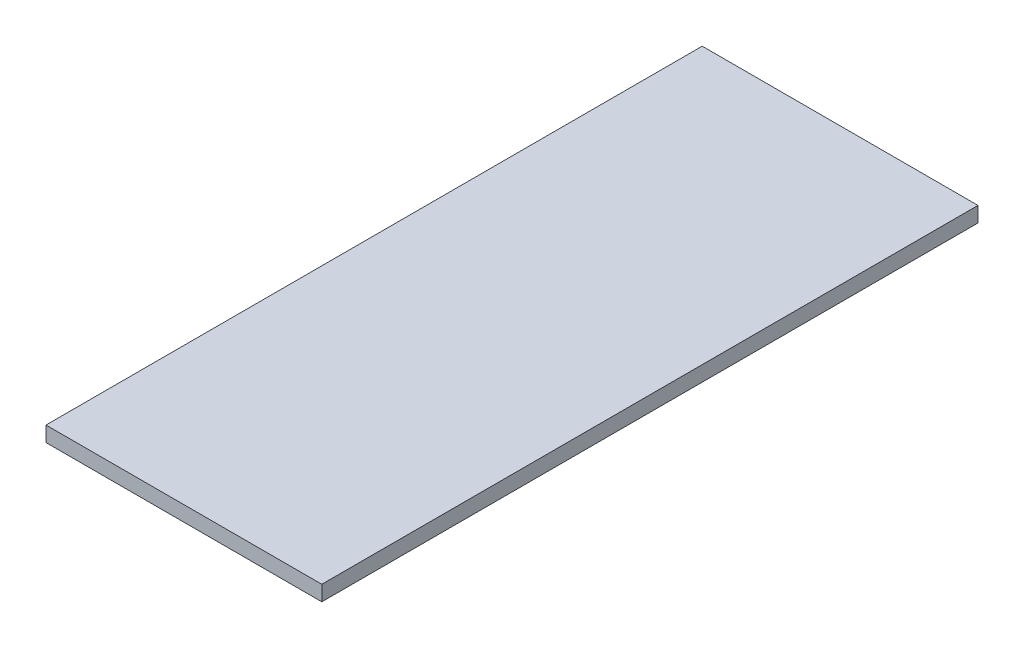
SolidWorks part; units mm, degrees
ref_plane "Front Plane" through (0, 0, 0) normal (0, 0, 1) x (1, 0, 0)
ref_plane "Top Plane" through (0, 0, 0) normal (0, 1, 0) x (1, 0, 0)
ref_plane "Right Plane" through (0, 0, 0) normal (1, 0, 0) x (0, 0, -1)
sketch "Sketch1" plane through (0, 0, 0) normal (0, 1, 0) x (1, 0, 0)
  line L1 (0, 0) -> (290, 0)
  line L2 (0, 0) -> (0, 690)
  line L3 (0, 690) -> (290, 690)
  line L4 (290, 0) -> (290, 690)
  dimension "D1" = 690
  dimension "D2" = 290
extrude "Extrude1" add sketch "Sketch1" along normal blind 16
